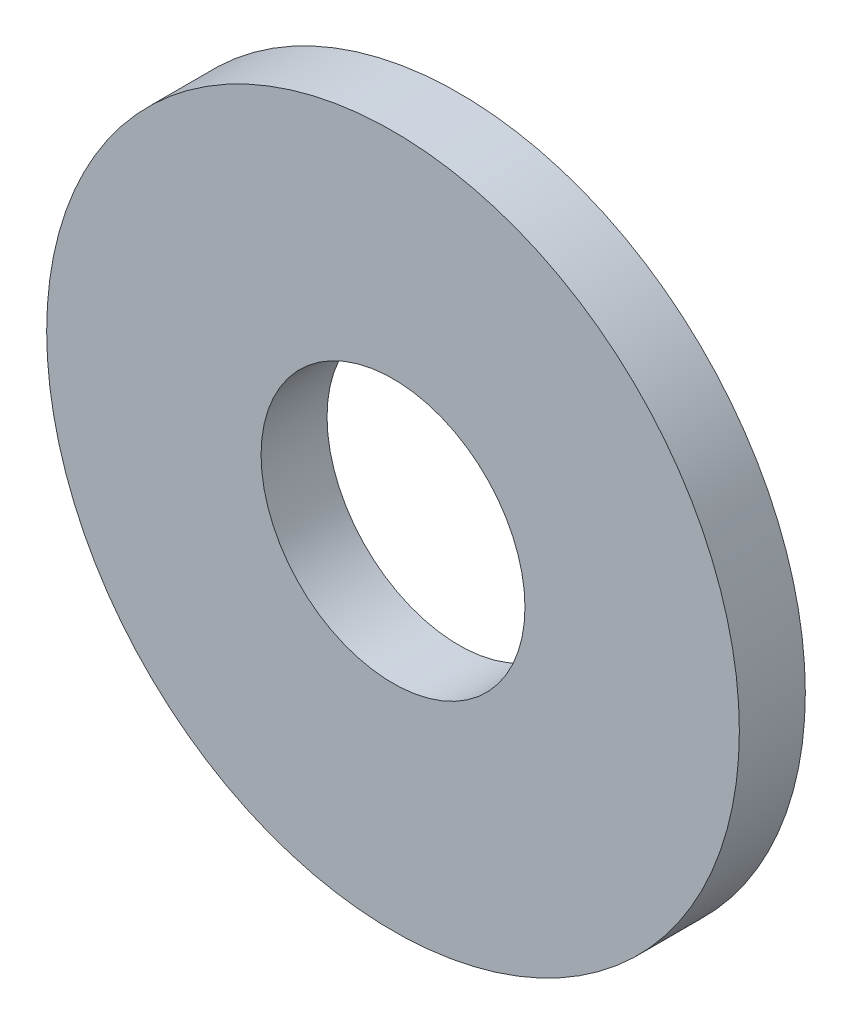
SolidWorks part; units mm, degrees
ref_plane "Front Plane" through (0, 0, 0) normal (0, 0, 1) x (1, 0, 0)
ref_plane "Top Plane" through (0, 0, 0) normal (0, 1, 0) x (1, 0, 0)
ref_plane "Right Plane" through (0, 0, 0) normal (1, 0, 0) x (0, 0, -1)
sketch "Sketch1" plane through (0, 0, 0) normal (0, 0, 1) x (1, 0, 0)
  circle A0 centre (0, 0) radius 4
  circle A1 centre (0, 0) radius 10.5
  dimension "D1" = 8
  dimension "D2" = 21
extrude "Boss-Extrude1" add sketch "Sketch1" along normal blind 2
